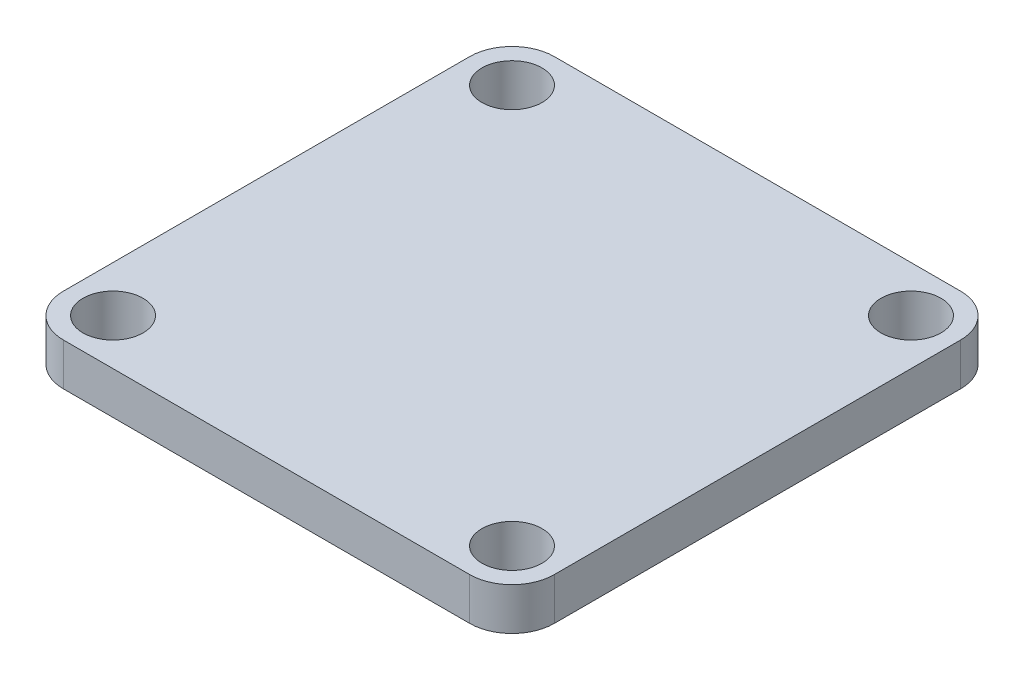
SolidWorks part; units mm, degrees
ref_plane "Front Plane" through (0, 0, 0) normal (0, 0, 1) x (1, 0, 0)
ref_plane "Top Plane" through (0, 0, 0) normal (0, 1, 0) x (1, 0, 0)
ref_plane "Right Plane" through (0, 0, 0) normal (1, 0, 0) x (0, 0, -1)
sketch "Sketch1" plane through (0, 0, 0) normal (0, 1, 0) x (1, 0, 0)
  line L0 (-23.57, 0) -> (23.57, 0) construction
  line L1 (-29, -29) -> (29, -29)
  line L2 (-29, -29) -> (-29, 29)
  line L3 (-29, 29) -> (29, 29)
  line L4 (29, -29) -> (29, 29)
  line L5 (-29, -29) -> (29, 29) construction
  line L6 (-29, 29) -> (29, -29) construction
  line L7 (-23.57, -29) -> (-23.57, -23.57) construction
  line L8 (-23.57, -23.57) -> (-29, -23.57) construction
  line L9 (0, -29) -> (0, 29) construction
  circle A0 centre (-23.57, -23.57) radius 2.55 construction
  circle A1 centre (23.57, -23.57) radius 2.55 construction
  circle A2 centre (23.57, 23.57) radius 2.55 construction
  circle A3 centre (-23.57, 23.57) radius 2.55 construction
  circle A4 centre (-23.57, 23.57) radius 3.55
  circle A5 centre (23.57, 23.57) radius 3.55
  circle A6 centre (23.57, -23.57) radius 3.55
  circle A7 centre (-23.57, -23.57) radius 3.55
  point P0 (0, 0)
  point P9 (0, 0)
  dimension "D3" = 5.1
  dimension "D4" = 7.1
  dimension "D1" = 58
  dimension "D2" = 47.14
extrude "Boss-Extrude1" add sketch "Sketch1" along normal blind 5
fillet "Fillet1" radius 5 4 edges at (29, 2.5, -29) (-29, 2.5, -29) (29, 2.5, 29) (-29, 2.5, 29)
